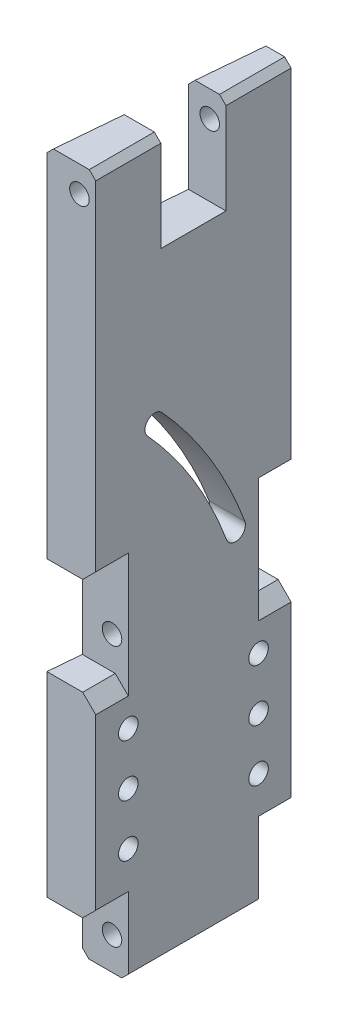
SolidWorks part; units mm, degrees
ref_plane "Front Plane" through (0, 0, 0) normal (0, 0, 1) x (1, 0, 0)
ref_plane "Top Plane" through (0, 0, 0) normal (0, 1, 0) x (1, 0, 0)
ref_plane "Right Plane" through (0, 0, 0) normal (1, 0, 0) x (0, 0, -1)
sketch "Sketch1" plane through (0, 0, 0) normal (1, 0, 0) x (0, 0, -1)
  line L0 (0, 0) -> (0, 25.4)
  line L1 (0, 25.4) -> (-12.7, 25.4)
  line L2 (-12.7, 25.4) -> (-12.7, 101.6)
  line L3 (-12.7, 101.6) -> (0, 101.6)
  line L4 (0, 101.6) -> (0, 139.7)
  line L5 (-12.7, 279.4) -> (63.5, 279.4)
  line L6 (63.5, 279.4) -> (63.5, 139.7)
  line L7 (50.8, 101.6) -> (63.5, 101.6)
  line L8 (63.5, 101.6) -> (63.5, 25.4)
  line L9 (63.5, 25.4) -> (50.8, 25.4)
  line L10 (50.8, 25.4) -> (50.8, 0)
  line L11 (50.8, 0) -> (0, 0)
  line L12 (50.8, 139.7) -> (50.8, 101.6)
  line L13 (63.5, 139.7) -> (50.8, 139.7)
  line L14 (0, 139.7) -> (-12.7, 139.7)
  line L15 (-12.7, 139.7) -> (-12.7, 279.4)
  dimension "D1" = 76.2
  dimension "D2" = 12.7
  dimension "D3" = 50.8
  dimension "D4" = 279.4
  dimension "D5" = 25.4
  dimension "D6" = 101.6
  dimension "D7" = 38.1
extrude "Boss-Extrude1" add sketch "Sketch1" along normal blind 19.05
sketch "Sketch2" plane through (0, 0, 0) normal (0, 0, 1) x (1, 0, 0)
  line L0 (19.05, 101.6) -> (0, 101.6) construction
  line L1 (19.05, 139.7) -> (19.05, 101.6) construction
  circle A0 centre (12.7, 114.3) radius 3.81
  dimension "D1" = 12.7
  dimension "D2" = 6.35
extrude "Cut-Extrude1" cut sketch "Sketch2" against normal through all
sketch "Sketch3" plane through (0, 0, 0) normal (0, 0, 1) x (1, 0, 0)
  line L0 (19.05, 25.4) -> (19.05, 0) construction
  circle A0 centre (12.7, 12.7) radius 3.81
  dimension "D1" = 6.35
extrude "Cut-Extrude2" cut sketch "Sketch3" against normal through all
sketch "Sketch4" plane through (19.05, 0, 0) normal (1, 0, 0) x (0, 0, -1)
  line L0 (-12.7, 101.6) -> (-12.7, 25.4) construction
  line L2 (0, 0) -> (50.8, 0) construction
  arc A4 (10.3034, 183.1562) -> (41.8628, 131.5151) centre (-106.68, 76.2) cw construction
  arc A5 (45.4333, 132.8447) -> (13.1152, 185.7271) centre (-106.68, 76.2) ccw
  arc A6 (38.2924, 130.1855) -> (7.4915, 180.5853) centre (-106.68, 76.2) ccw
  arc A7 (38.2924, 130.1855) -> (45.4333, 132.8447) centre (41.8628, 131.5151) ccw
  arc A8 (13.1152, 185.7271) -> (7.4915, 180.5853) centre (10.3034, 183.1562) ccw
  point P11 (28.5707, 158.8559)
  dimension "D3" = 93.98
  dimension "D4" = 76.2
  dimension "D2" = 2
extrude "Cut-Extrude3" cut sketch "Sketch4" against normal through all
sketch "Sketch6" plane through (19.05, 0, 0) normal (1, 0, 0) x (0, 0, -1)
  circle A0 centre (0, 44.9044) radius 3.81
  circle A1 centre (50.8, 44.9044) radius 3.81
extrude "Cut-Extrude4" cut sketch "Sketch6" against normal through all
pattern_linear "LPattern1" count 3 spacing 20.32 along (0, 1, 0) of "Cut-Extrude4"
sketch "Sketch7" plane through (19.05, 0, 0) normal (1, 0, 0) x (0, 0, -1)
  line L0 (63.5, 279.4) -> (-12.7, 279.4) construction
  line L1 (25.4, 241.3) -> (25.4, 0) construction
  line L2 (12.7, 279.4) -> (38.1, 279.4)
  line L3 (12.7, 279.4) -> (12.7, 241.3)
  line L4 (12.7, 241.3) -> (38.1, 241.3)
  line L5 (38.1, 279.4) -> (38.1, 241.3)
  line L6 (0, 0) -> (50.8, 0) construction
  dimension "D1" = 25.4
  dimension "D2" = 38.1
extrude "Cut-Extrude5" cut sketch "Sketch7" against normal through all
sketch "Sketch8" plane through (0, 0, 0) normal (0, 1, 0) x (1, 0, 0)
  line L0 (0, 63.5) -> (6.6666, 63.5)
  line L3 (0, -12.7) -> (0, 63.5)
  line L4 (19.05, 63.5) -> (0, 63.5) construction
  line L5 (6.6666, 63.5) -> (0, -12.7)
  dimension "D1" = 5
extrude "Cut-Extrude6" cut sketch "Sketch8" along normal through all
sketch "Sketch9" plane through (0, 0, 0) normal (0, 0, 1) x (1, 0, 0)
  line L0 (19.05, 139.7) -> (19.05, 101.6) construction
  line L1 (19.05, 279.4) -> (1.1111, 279.4) construction
  circle A0 centre (12.7, 269.24) radius 3.81
  dimension "D1" = 6.35
  dimension "D2" = 10.16
extrude "Cut-Extrude7" cut sketch "Sketch9" against normal mid plane 152.4
chamfer "Chamfer1" distance 2.54 angle 45 6 edges at (5.5555, 279.4, -50.8) (1.1111, 279.4, 0) (19.05, 279.4, -50.8) (19.05, 279.4, 0) (3.3333, 0, -25.4) (19.05, 0, -25.4)
chamfer "Chamfer2" distance 5.08 angle 45 6 edges at (19.05, 25.4, 6.35) (19.05, 25.4, -57.15) (19.05, 101.6, -57.15) (19.05, 139.7, -57.15) (19.05, 139.7, 6.35) (19.05, 101.6, 6.35)
